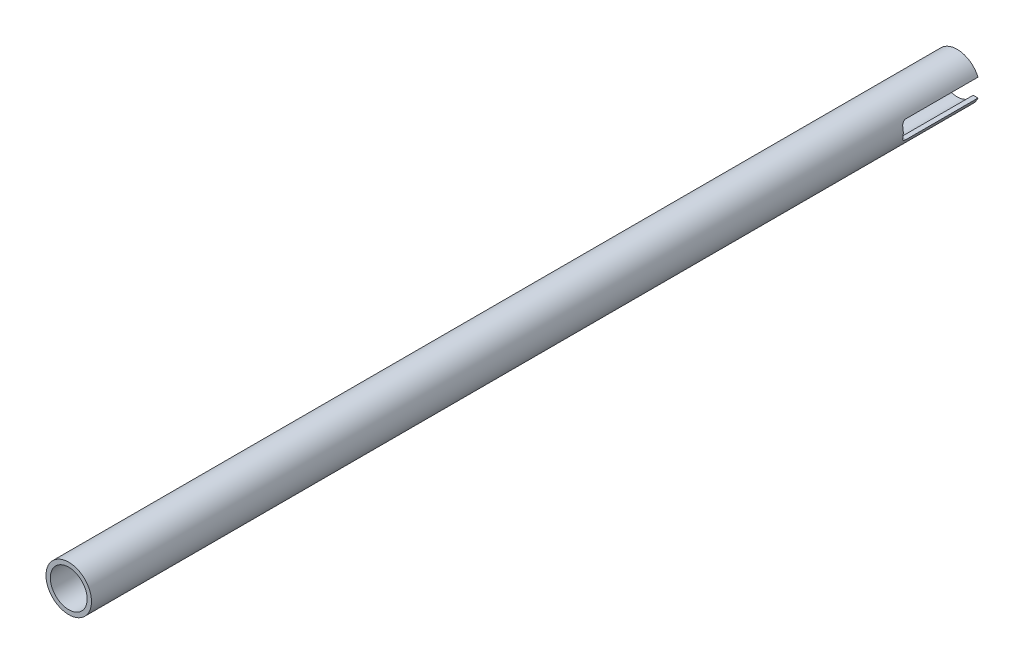
SolidWorks part; units mm, degrees
material "AISI 4130 Steel, annealed at 865C"
ref_plane "Front Plane" through (0, 0, 0) normal (0, 0, 1) x (1, 0, 0)
ref_plane "Top Plane" through (0, 0, 0) normal (0, 1, 0) x (1, 0, 0)
ref_plane "Right Plane" through (0, 0, 0) normal (1, 0, 0) x (0, 0, -1)
sketch "Sketch1" plane through (0, 0, 0) normal (0, 0, 1) x (1, 0, 0)
  circle A0 centre (0, 0) radius 6.477
  circle A1 centre (0, 0) radius 8.001
  dimension "D1" = 12.954
  dimension "D2" = 16.002
extrude "Boss-Extrude1" add sketch "Sketch1" along normal blind 312.42
sketch "Sketch2" plane through (0, 0, 0) normal (1, 0, 0) x (0, 0, -1)
  line L0 (0, 3.175) -> (-25.4, 3.175)
  line L1 (0, 8.8011) -> (0, -8.8011) construction
  line L2 (-25.4, -3.175) -> (0, -3.175)
  line L3 (-26.924, 1.651) -> (-26.924, -1.651)
  line L4 (0, -8.001) -> (0, 8.001) construction
  arc A0 (-26.924, 1.651) -> (-25.4, 3.175) centre (-25.4, 1.651) cw
  arc A1 (-25.4, -3.175) -> (-26.924, -1.651) centre (-25.4, -1.651) cw
  dimension "D5" = 25.4
  dimension "D6" = 26.924
  dimension "D1" = 26.924
  dimension "D2" = 25.4
  dimension "D3" = 6.35
  dimension "D4" = 3.175
extrude "Cut-Extrude2" cut sketch "Sketch2" against normal through all both and the other way through all
